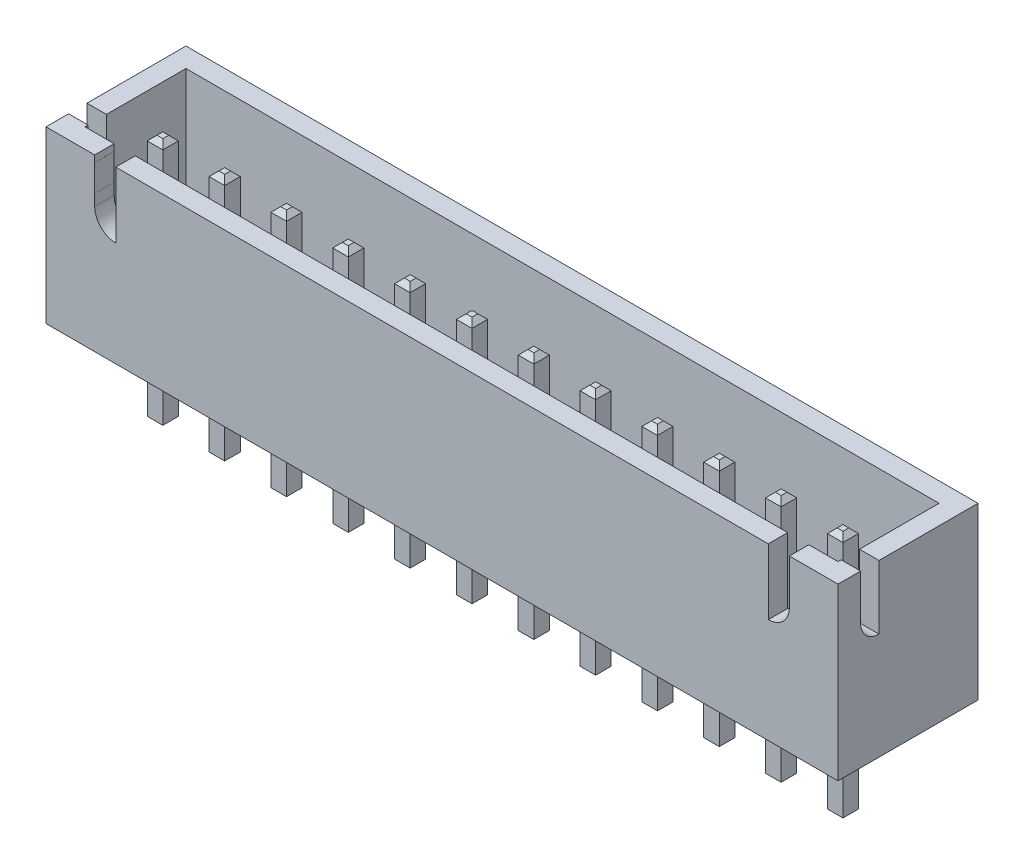
SolidWorks part; units mm, degrees
other "Camera1"
ref_plane "Front Plane" through (0, 0, 0) normal (0, 0, 1) x (1, 0, 0)
ref_plane "Top Plane" through (0, 0, 0) normal (0, 1, 0) x (1, 0, 0)
ref_plane "Right Plane" through (0, 0, 0) normal (1, 0, 0) x (0, 0, -1)
sketch "Sketch1" plane through (0, 0, 0) normal (0, 1, 0) x (1, 0, 0)
  line L1 (-16.2687, 2.875) -> (16.2687, 2.875)
  line L2 (-16.2687, 2.875) -> (-16.2687, -2.875)
  line L3 (-16.2687, -2.875) -> (16.2687, -2.875)
  line L4 (16.2687, 2.875) -> (16.2687, -2.875)
  line L5 (-16.2687, 2.875) -> (16.2687, -2.875) construction
  line L6 (-16.2687, -2.875) -> (16.2687, 2.875) construction
  point P0 (0, 0)
  dimension "D1" = 5.75
  dimension "D2" = 32.5374
extrude "Boss-Extrude1" add sketch "Sketch1" along normal blind 7
shell "Shell1" thickness 0.8
sketch "Sketch2" plane through (16.2687, 0, 0) normal (1, 0, 0) x (0, 0, -1)
  line L0 (-1.193, 7) -> (-1.193, 4.3796)
  line L1 (-2.875, 7) -> (2.875, 7) construction
  line L2 (-1.9469, 5.1335) -> (-1.9469, 7)
  line L3 (-1.9469, 7) -> (-1.193, 7)
  arc A0 (-1.193, 4.3796) -> (-1.9469, 5.1335) centre (-1.193, 5.1335) cw
extrude "Cut-Extrude1" cut sketch "Sketch2" against normal through all
sketch "Sketch3" plane through (0, 0, 2.875) normal (0, 0, 1) x (1, 0, 0)
  line L0 (-14.2687, 7) -> (-14.2687, 6.7289)
  line L1 (-16.2687, 7) -> (16.2687, 7) construction
  line L2 (-14.2687, 6.7289) -> (-14.2681, 6.7289)
  line L3 (-14.2681, 6.7289) -> (-14.2687, 5.6299)
  line L4 (-14.2687, 5.6299) -> (-14.2687, 5.1663)
  line L5 (-13.4025, 4.3001) -> (-13.4025, 7)
  line L6 (-13.4025, 7) -> (-14.2687, 7)
  line L7 (-16.2687, 7) -> (-16.2687, 0) construction
  line L8 (0, 7) -> (0, 0) construction
  line L9 (13.4025, 7) -> (14.2687, 7)
  line L10 (13.4025, 4.3001) -> (13.4025, 7)
  line L11 (14.2687, 5.6299) -> (14.2687, 5.1663)
  line L12 (14.2681, 6.7289) -> (14.2687, 5.6299)
  line L13 (14.2687, 6.7289) -> (14.2681, 6.7289)
  line L14 (14.2687, 7) -> (14.2687, 6.7289)
  arc A0 (-14.2687, 5.1663) -> (-13.4025, 4.3001) centre (-13.4025, 5.1663) ccw
  arc A1 (14.2687, 5.1663) -> (13.4025, 4.3001) centre (13.4025, 5.1663) cw
  dimension "D1" = 2
extrude "Cut-Extrude2" cut sketch "Sketch3" against normal up to next
sketch "Sketch4" plane through (0, 0, 0) normal (0, -1, 0) x (1, 0, 0)
  line L0 (-16.2687, -2.875) -> (-16.2687, 2.875) construction
  line L1 (-14.1387, 0.845) -> (-13.4987, 0.845)
  line L2 (-14.1387, 0.845) -> (-14.1387, 0.205)
  line L3 (-14.1387, 0.205) -> (-13.4987, 0.205)
  line L4 (-13.4987, 0.845) -> (-13.4987, 0.205)
  line L5 (-14.1387, 0.845) -> (-13.4987, 0.205) construction
  line L6 (-14.1387, 0.205) -> (-13.4987, 0.845) construction
  line L7 (-11.5987, 0.205) -> (-10.9587, 0.205)
  line L8 (-11.5987, 0.845) -> (-11.5987, 0.205)
  line L9 (-16.2687, 2.875) -> (16.2687, 2.875) construction
  line L10 (-11.5987, 0.845) -> (-10.9587, 0.845)
  line L11 (-10.9587, 0.845) -> (-10.9587, 0.205)
  line L12 (-9.0587, 0.205) -> (-8.4187, 0.205)
  line L13 (-9.0587, 0.845) -> (-9.0587, 0.205)
  line L14 (-9.0587, 0.845) -> (-8.4187, 0.845)
  line L15 (-8.4187, 0.845) -> (-8.4187, 0.205)
  line L16 (-6.5187, 0.205) -> (-5.8787, 0.205)
  line L17 (-6.5187, 0.845) -> (-6.5187, 0.205)
  line L18 (-6.5187, 0.845) -> (-5.8787, 0.845)
  line L19 (-5.8787, 0.845) -> (-5.8787, 0.205)
  line L20 (-3.9787, 0.205) -> (-3.3387, 0.205)
  line L21 (-3.9787, 0.845) -> (-3.9787, 0.205)
  line L22 (-3.9787, 0.845) -> (-3.3387, 0.845)
  line L23 (-3.3387, 0.845) -> (-3.3387, 0.205)
  line L24 (-1.4387, 0.205) -> (-0.7987, 0.205)
  line L25 (-1.4387, 0.845) -> (-1.4387, 0.205)
  line L26 (-1.4387, 0.845) -> (-0.7987, 0.845)
  line L27 (-0.7987, 0.845) -> (-0.7987, 0.205)
  line L28 (1.1013, 0.205) -> (1.7413, 0.205)
  line L29 (1.1013, 0.845) -> (1.1013, 0.205)
  line L30 (1.1013, 0.845) -> (1.7413, 0.845)
  line L31 (1.7413, 0.845) -> (1.7413, 0.205)
  line L32 (3.6413, 0.205) -> (4.2813, 0.205)
  line L33 (3.6413, 0.845) -> (3.6413, 0.205)
  line L34 (3.6413, 0.845) -> (4.2813, 0.845)
  line L35 (4.2813, 0.845) -> (4.2813, 0.205)
  line L36 (6.1813, 0.205) -> (6.8213, 0.205)
  line L37 (6.1813, 0.845) -> (6.1813, 0.205)
  line L38 (6.1813, 0.845) -> (6.8213, 0.845)
  line L39 (6.8213, 0.845) -> (6.8213, 0.205)
  line L40 (8.7213, 0.205) -> (9.3613, 0.205)
  line L41 (8.7213, 0.845) -> (8.7213, 0.205)
  line L42 (8.7213, 0.845) -> (9.3613, 0.845)
  line L43 (9.3613, 0.845) -> (9.3613, 0.205)
  line L44 (11.2613, 0.205) -> (11.9013, 0.205)
  line L45 (11.2613, 0.845) -> (11.2613, 0.205)
  line L46 (11.2613, 0.845) -> (11.9013, 0.845)
  line L47 (11.9013, 0.845) -> (11.9013, 0.205)
  line L48 (13.8013, 0.205) -> (14.4413, 0.205)
  line L49 (13.8013, 0.845) -> (13.8013, 0.205)
  line L50 (13.8013, 0.845) -> (14.4413, 0.845)
  line L51 (14.4413, 0.845) -> (14.4413, 0.205)
  point P0 (-13.8187, 0.525)
  dimension "D1" = 0.64
  dimension "D2" = 0.64
  dimension "D3" = 2.45
  dimension "D4" = 2.35
  dimension "D5" = 12
extrude "Boss-Extrude2" add sketch "Sketch4" along normal blind 3.45 and the other way blind 6.75
chamfer "Chamfer1" distance 0.2 angle 45 96 edges at (-13.8187, -3.45, 0.205) (-14.1387, -3.45, 0.525) (-13.8187, -3.45, 0.845) (-13.4987, -3.45, 0.525) (-13.8187, 6.75, 0.845) (-14.1387, 6.75, 0.525) (-13.8187, 6.75, 0.205) (-13.4987, 6.75, 0.525) (-11.2787, -3.45, 0.205) (-11.5987, -3.45, 0.525) (-11.2787, -3.45, 0.845) (-10.9587, -3.45, 0.525) (-8.7387, -3.45, 0.205) (-9.0587, -3.45, 0.525) (-8.7387, -3.45, 0.845) (-8.4187, -3.45, 0.525) (-6.1987, -3.45, 0.205) (-6.5187, -3.45, 0.525) (-6.1987, -3.45, 0.845) (-5.8787, -3.45, 0.525) (-3.6587, -3.45, 0.205) (-3.9787, -3.45, 0.525) (-3.6587, -3.45, 0.845) (-3.3387, -3.45, 0.525) (-1.1187, -3.45, 0.205) (-1.4387, -3.45, 0.525) (-1.1187, -3.45, 0.845) (-0.7987, -3.45, 0.525) (14.1213, -3.45, 0.205) (13.8013, -3.45, 0.525) (14.1213, -3.45, 0.845) (14.4413, -3.45, 0.525) (1.4213, -3.45, 0.205) (1.1013, -3.45, 0.525) (1.4213, -3.45, 0.845) (1.7413, -3.45, 0.525) (3.9613, -3.45, 0.205) (3.6413, -3.45, 0.525) (3.9613, -3.45, 0.845) (4.2813, -3.45, 0.525) (6.5013, -3.45, 0.205) (6.1813, -3.45, 0.525) (6.5013, -3.45, 0.845) (6.8213, -3.45, 0.525) (9.0413, -3.45, 0.205) (8.7213, -3.45, 0.525) (9.0413, -3.45, 0.845) (9.3613, -3.45, 0.525) (11.5813, -3.45, 0.205) (11.2613, -3.45, 0.525) (11.5813, -3.45, 0.845) (11.9013, -3.45, 0.525) (14.1213, 6.75, 0.845) (13.8013, 6.75, 0.525) (14.1213, 6.75, 0.205) (14.4413, 6.75, 0.525) (11.5813, 6.75, 0.845) (11.2613, 6.75, 0.525) (11.5813, 6.75, 0.205) (11.9013, 6.75, 0.525) (9.0413, 6.75, 0.845) (8.7213, 6.75, 0.525) (9.0413, 6.75, 0.205) (9.3613, 6.75, 0.525) (6.5013, 6.75, 0.845) (6.1813, 6.75, 0.525) (6.5013, 6.75, 0.205) (6.8213, 6.75, 0.525) (3.9613, 6.75, 0.845) (3.6413, 6.75, 0.525) (3.9613, 6.75, 0.205) (4.2813, 6.75, 0.525) (1.4213, 6.75, 0.845) (1.1013, 6.75, 0.525) (1.4213, 6.75, 0.205) (1.7413, 6.75, 0.525) (-1.1187, 6.75, 0.845) (-1.4387, 6.75, 0.525) (-1.1187, 6.75, 0.205) (-0.7987, 6.75, 0.525) (-3.6587, 6.75, 0.845) (-3.9787, 6.75, 0.525) (-3.6587, 6.75, 0.205) (-3.3387, 6.75, 0.525) (-6.1987, 6.75, 0.845) (-6.5187, 6.75, 0.525) (-6.1987, 6.75, 0.205) (-5.8787, 6.75, 0.525) (-8.7387, 6.75, 0.845) (-9.0587, 6.75, 0.525) (-8.7387, 6.75, 0.205) (-8.4187, 6.75, 0.525) (-11.2787, 6.75, 0.845) (-11.5987, 6.75, 0.525) (-11.2787, 6.75, 0.205) (-10.9587, 6.75, 0.525)
